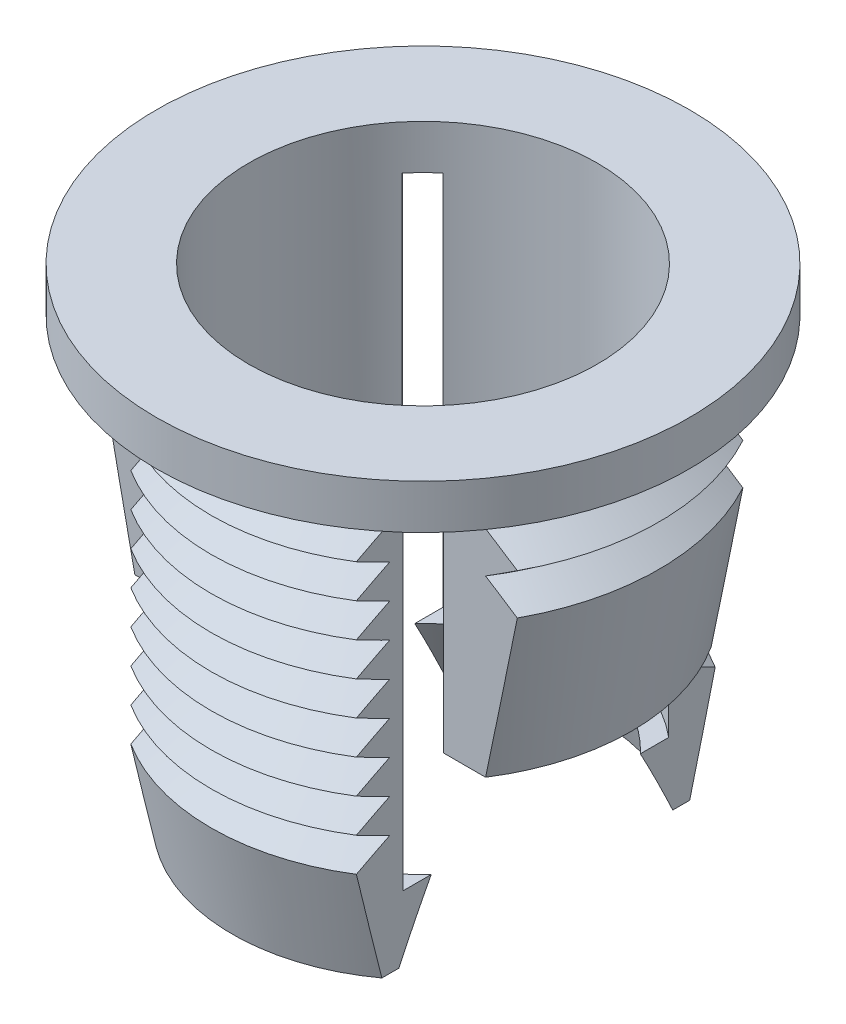
SolidWorks part; units mm, degrees
ref_plane "Front" through (0, 0, 0) normal (0, 0, 1) x (1, 0, 0)
ref_plane "Top" through (0, 0, 0) normal (0, 1, 0) x (1, 0, 0)
ref_plane "Right" through (0, 0, 0) normal (1, 0, 0) x (0, 0, -1)
curve "x-axis"
  spline degree 1 poles (0, 0, 0) (100, 0, 0) knots 0 0 1 1
curve "y-axis"
  spline degree 1 poles (0, 0, 0) (0, 100, 0) knots 0 0 1 1
curve "z-axis"
  spline degree 1 poles (0, 0, 0) (0, 0, 100) knots 0 0 1 1
sketch "Sketch1" plane through (0, 0, 0) normal (0, 1, 0) x (1, 0, 0)
  line L0 (0, 0) -> (12.526, 0) construction
  line L1 (0, 0) -> (0, 13.2596) construction
  circle A0 centre (0, 0) radius 3.9
  circle A1 centre (0, 0) radius 2.55
  dimension "D1" = 7.8
  dimension "D2" = 5.1
extrude "Boss-Extrude1" add sketch "Sketch1" along normal blind 0.65
sketch "Sketch2" plane through (0, 0, 0) normal (0, 0, 1) x (1, 0, 0)
  line L0 (3.9, 0.65) -> (2.55, 0.65)
  line L1 (-2.55, 0.65) -> (-3.9, 0.65)
  line L2 (-2.55, 0.65) -> (-3.9, 0.65) construction
  line L3 (0, 0) -> (0, -3.75) construction
  line L4 (3.9, 0) -> (2.55, 0)
  line L5 (-2.55, 0) -> (-3.9, 0)
  line L6 (-2.55, 0) -> (-3.05, 0)
  line L7 (-2.55, -3.75) -> (-3.05, -3.75)
  line L8 (-3.05, -3.75) -> (-3.45, -1.5)
  line L9 (-3.45, -1.5) -> (-3.05, -1.2)
  line L10 (-3.05, -1.2) -> (-3.45, -0.9)
  line L11 (-3.45, -0.9) -> (-3.05, -0.6)
  line L12 (-3.05, -0.6) -> (-3.45, -0.3)
  line L13 (-3.45, -0.3) -> (-3.05, 0)
  line L14 (-3.05, 0) -> (-3.05, -4.4377) construction
  line L15 (-3.45, -1.5) -> (-3.45, 0) construction
  line L16 (-2.55, 0) -> (-2.55, 0.65)
  line L17 (2.55, 0.65) -> (2.55, 0)
  line L18 (-2.55, 0) -> (-2.55, -3.75)
  line L19 (-2.55, 0) -> (-2.55, 0.65) construction
  dimension "D1" = 4.4
  dimension "D2" = 3.05
  dimension "D3" = 3.45
  dimension "D4" = 2.25
  dimension "D5" = 1.5
  dimension "D6" = 0.3
  dimension "D7" = 0.3
  dimension "D8" = 0.3
  dimension "D9" = 0.3
  dimension "D10" = 0.3
revolve "Revolve1" add sketch "Sketch2" angle 360 about L3
sketch "Sketch3" plane through (0, 0, 0) normal (0, 0, 1) x (1, 0, 0)
  line L0 (0, 0) -> (0, -10.6111) construction
  line L1 (0, 0) -> (7.9835, 0) construction
  line L2 (-1.95, 0) -> (1.95, 0)
  line L3 (-1.95, 0) -> (-1.95, -6)
  line L4 (-1.95, -6) -> (1.95, -6)
  line L5 (1.95, 0) -> (1.95, -6)
  dimension "D1" = 3.9
  dimension "D2" = 1.95
  dimension "D3" = 6
extrude "Cut-Extrude1" cut sketch "Sketch3" against normal through all both and the other way through all
sketch "Sketch4" plane through (0, 0, 0) normal (1, 0, 0) x (0, 0, -1)
  line L0 (0, 0) -> (6.1596, 0) construction
  line L1 (0, 0) -> (0, -8.8851) construction
  line L3 (-4.65, 0) -> (-1.65, 0)
  line L4 (-4.65, 0) -> (-4.65, -9)
  line L5 (-4.65, -9) -> (-1.65, -9)
  line L6 (-1.65, 0) -> (-1.65, -9)
  line L7 (1.65, 0) -> (4.65, 0)
  line L8 (1.65, 0) -> (1.65, -9)
  line L9 (1.65, -9) -> (4.65, -9)
  line L10 (4.65, 0) -> (4.65, -9)
  dimension "D1" = 1.65
  dimension "D2" = 1.65
  dimension "D3" = 3
  dimension "D4" = 3
  dimension "D5" = 9
extrude "Cut-Extrude2" cut sketch "Sketch4" against normal through all both and the other way through all
sketch "Sketch5" plane through (0, 0, 0) normal (1, 0, 0) x (0, 0, -1)
  line L0 (0, 0) -> (7.6592, 0) construction
  line L1 (0, 0) -> (0, -11.464) construction
  line L2 (3.1, -4.95) -> (2.7, -4.7025)
  line L3 (2.7, -4.7025) -> (3.1, -4.455)
  line L4 (3.1, 0) -> (3.1, -7.7329) construction
  line L5 (2.7, -4.2075) -> (3.1, -3.96)
  line L6 (3.1, -4.455) -> (2.7, -4.2075)
  line L7 (2.7, -3.7125) -> (3.1, -3.465)
  line L8 (3.1, -3.96) -> (2.7, -3.7125)
  line L9 (2.7, -3.2175) -> (3.1, -2.97)
  line L10 (0, -6.45) -> (2.7915, -6.45)
  line L11 (0, 0) -> (0, -6.45)
  line L12 (2.7915, -6.45) -> (3.1, -4.95)
  line L14 (3.1, -3.465) -> (2.7, -3.2175)
  line L15 (2.7, -2.7225) -> (3.1, -2.475)
  line L16 (3.1, -2.97) -> (2.7, -2.7225)
  line L17 (2.7, -2.2275) -> (3.1, -1.98)
  line L18 (3.1, -2.475) -> (2.7, -2.2275)
  line L19 (2.7, -1.7325) -> (3.1, -1.485)
  line L20 (3.1, -1.98) -> (2.7, -1.7325)
  line L21 (2.7, -1.2375) -> (3.1, -0.99)
  line L22 (3.1, -1.485) -> (2.7, -1.2375)
  line L23 (2.7, -0.7425) -> (3.1, -0.495)
  line L24 (3.1, -0.99) -> (2.7, -0.7425)
  line L25 (2.7, -0.2475) -> (3.1, 0)
  line L26 (3.1, -0.495) -> (2.7, -0.2475)
  line L27 (3.1, 0) -> (0, 0)
  line L28 (3.9, 0.65) -> (2.55, 0.65)
  line L29 (-2.55, 0.65) -> (-3.9, 0.65)
  line L31 (3.9, 0.65) -> (2.55, 0.65) construction
  point P12 (-1.7599, -6.45)
  point P14 (4.7544, -6.45)
  dimension "D1" = 3.1
  dimension "D2" = 1.5
  dimension "D5" = 0.2475
  dimension "D6" = 0.4
  dimension "D7" = 7.1
revolve "Revolve2" add sketch "Sketch5" angle 360 about L11
sketch "Sketch6" plane through (0, 0, 0) normal (0, 1, 0) x (1, 0, 0)
  circle A0 centre (0, 0) radius 2.55
  dimension "D1" = 5.1
extrude "Cut-Extrude3" cut sketch "Sketch6" against normal blind 5.5
sketch "Sketch7" plane through (0, 0, 0) normal (0, 0, 1) x (1, 0, 0)
  line L0 (0, 0) -> (5.65, 0) construction
  line L1 (0, 0) -> (0, -12.8368) construction
  line L3 (1.65, 0) -> (5.65, 0)
  line L4 (1.65, 0) -> (1.65, -8)
  line L5 (1.65, -8) -> (5.65, -8)
  line L6 (5.65, 0) -> (5.65, -8)
  line L7 (-1.65, 0) -> (-5.65, 0)
  line L8 (-1.65, 0) -> (-1.65, -8)
  line L9 (-1.65, -8) -> (-5.65, -8)
  line L10 (-5.65, 0) -> (-5.65, -8)
  dimension "D1" = 3.3
  dimension "D2" = 1.65
  dimension "D3" = 4
  dimension "D4" = 4
  dimension "D5" = 8
extrude "Cut-Extrude5" cut sketch "Sketch7" against normal through all both and the other way through all
sketch "Sketch9" plane through (0, -5.5, 0) normal (0, 1, 0) x (1, 0, 0)
  circle A0 centre (0, 0) radius 2.25
  dimension "D1" = 4.5
extrude "Cut-Extrude6" cut sketch "Sketch9" against normal blind 5.5 draft 20 draft outward yes
combine bodies "Combine1" operation type add bodies to combine 104 111 110
